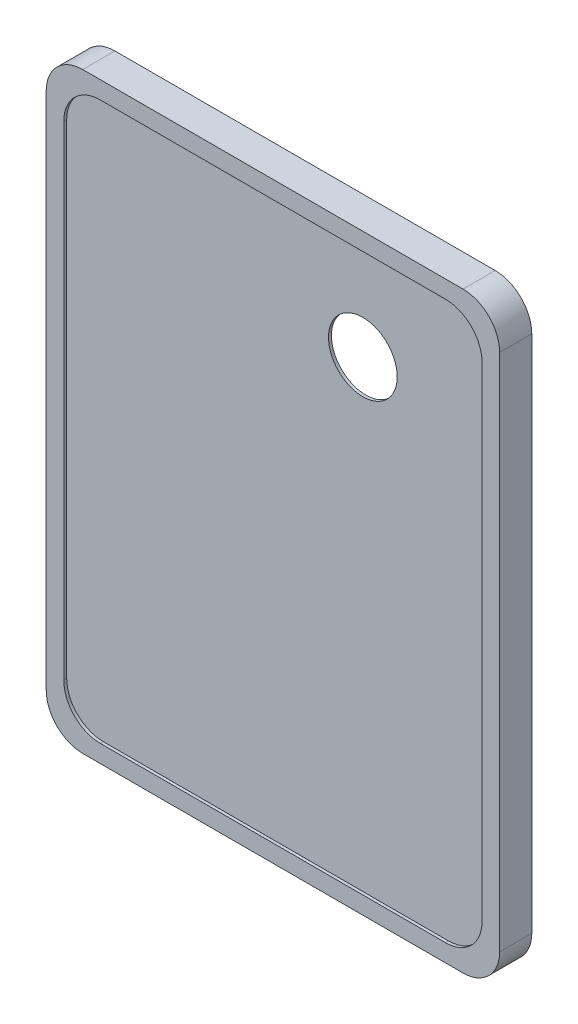
SolidWorks part; units mm, degrees
material "Nickel"
ref_plane "Front Plane" through (0, 0, 0) normal (0, 0, 1) x (1, 0, 0)
ref_plane "Top Plane" through (0, 0, 0) normal (0, 1, 0) x (1, 0, 0)
ref_plane "Right Plane" through (0, 0, 0) normal (1, 0, 0) x (0, 0, -1)
sketch "Sketch1" plane through (0, 0, 0) normal (0, 0, 1) x (1, 0, 0)
  line L1 (-33.02, 51.435) -> (33.02, 51.435)
  line L2 (-39.37, 45.085) -> (-39.37, -45.085)
  line L3 (-33.02, -51.435) -> (33.02, -51.435)
  line L4 (39.37, 45.085) -> (39.37, -45.085)
  line L5 (-39.37, 51.435) -> (39.37, -51.435) construction
  line L6 (-39.37, -51.435) -> (39.37, 51.435) construction
  arc A0 (-39.37, -45.085) -> (-33.02, -51.435) centre (-33.02, -45.085) ccw
  arc A1 (33.02, -51.435) -> (39.37, -45.085) centre (33.02, -45.085) ccw
  arc A2 (39.37, 45.085) -> (33.02, 51.435) centre (33.02, 45.085) ccw
  arc A3 (-33.02, 51.435) -> (-39.37, 45.085) centre (-33.02, 45.085) ccw
  point P0 (0, 0)
  dimension "D3" = 6.35
  dimension "D1" = 102.87
  dimension "D2" = 78.74
extrude "Boss-Extrude1" add sketch "Sketch1" along normal blind 5.588
sketch "Sketch2" plane through (0, 0, 5.588) normal (0, 0, 1) x (1, 0, 0)
  line L0 (39.37, -45.085) -> (39.37, 45.085) construction
  line L1 (-29.972, -48.387) -> (29.972, -48.387)
  line L2 (-36.322, -42.037) -> (-36.322, 42.037)
  line L3 (-29.972, 48.387) -> (29.972, 48.387)
  line L4 (36.322, -42.037) -> (36.322, 42.037)
  line L5 (-36.322, -48.387) -> (36.322, 48.387) construction
  line L6 (-36.322, 48.387) -> (36.322, -48.387) construction
  line L7 (-33.02, -51.435) -> (33.02, -51.435) construction
  arc A0 (-36.322, -42.037) -> (-29.972, -48.387) centre (-29.972, -42.037) ccw
  arc A1 (29.972, -48.387) -> (36.322, -42.037) centre (29.972, -42.037) ccw
  arc A2 (36.322, 42.037) -> (29.972, 48.387) centre (29.972, 42.037) ccw
  arc A3 (-29.972, 48.387) -> (-36.322, 42.037) centre (-29.972, 42.037) ccw
  point P0 (0, 0)
  dimension "D3" = 6.35
  dimension "D1" = 3.048
  dimension "D2" = 3.048
extrude "Cut-Extrude1" cut sketch "Sketch2" against normal blind 0.508
shell "Shell2" thickness 0.508
sketch "Sketch3" plane through (0, 0, 5.08) normal (0, 0, 1) x (1, 0, 0)
  line L0 (39.37, -45.085) -> (39.37, 45.085) construction
  line L1 (33.02, 51.435) -> (-33.02, 51.435) construction
  circle A0 centre (15.113, 32.004) radius 5.969
  dimension "D3" = 11.938
  dimension "D1" = 18.288
  dimension "D2" = 25.4
extrude "Cut-Extrude2" cut sketch "Sketch3" against normal blind 0.508
ref_plane "Plane1" through (39.37, -45.085, 0) normal (0, 1, 0) x (1, 0, 0)
sketch "Sketch5" plane through (39.37, 0, 0) normal (1, 0, 0) x (0, 0, -1)
  line L0 (0, -51.435) -> (2.54, -51.435)
  line L1 (2.54, -51.435) -> (2.54, -50.927)
  line L2 (2.54, -50.927) -> (0, -50.927)
  line L3 (0, -51.435) -> (0, -45.085) construction
  line L4 (0, -50.927) -> (0, -51.435)
  dimension "D1" = 0.508
  dimension "D2" = 2.54
extrude "Boss-Extrude2" add sketch "Sketch5" against normal blind 76.708
sketch "Sketch7" plane through (39.37, 0, 0) normal (1, 0, 0) x (0, 0, -1)
  line L0 (2.54, -50.927) -> (0, -50.927) construction
  circle A0 centre (1.524, -52.197) radius 1.27
  dimension "D1" = 2.54
extrude "Boss-Extrude3" add sketch "Sketch7" against normal blind 76.708
sketch "Sketch8" plane through (39.37, 0, 0) normal (1, 0, 0) x (0, 0, -1)
  line L0 (1.524, -50.927) -> (2.54, -50.927)
  line L1 (2.54, -50.927) -> (2.54, -51.435)
  circle A0 centre (1.524, -52.197) radius 1.27
  line M3 (2.54, -51.435) -> (2.54, -50.927)
  line M4 (2.54, -50.927) -> (0, -50.927)
extrude "Cut-Extrude3" cut sketch "Sketch8" against normal through all contours A0 M3 M4
sketch "Sketch9" plane through (39.37, 0, 0) normal (1, 0, 0) x (0, 0, -1)
  circle A0 centre (1.524, -52.197) radius 1.016
  dimension "D1" = 2.032
extrude "Cut-Extrude4" cut sketch "Sketch9" against normal through all
sketch "Sketch10" plane through (0, 0, 5.588) normal (0, 0, 1) x (1, 0, 0)
  line L0 (-33.02, -51.435) -> (33.02, -51.435) construction
  line L1 (39.37, -51.435) -> (24.892, -51.435)
  line L2 (39.37, -51.435) -> (39.37, -54.461)
  line L3 (39.37, -54.461) -> (24.892, -54.461)
  line L4 (24.892, -51.435) -> (24.892, -54.461)
  line L5 (-37.338, -53.467) -> (-24.638, -53.467)
  line L6 (-37.338, -53.467) -> (-37.338, -51.435)
  line L7 (-37.338, -51.435) -> (-24.638, -51.435)
  line L8 (-24.638, -53.467) -> (-24.638, -51.435)
  line L9 (-37.338, -53.467) -> (39.37, -53.467) construction
  line L10 (-17.526, -53.467) -> (-10.414, -53.467)
  line L11 (-17.526, -53.467) -> (-17.526, -51.435)
  line L12 (-35.5087, -50.927) -> (-37.338, -50.927)
  line L13 (-37.338, -50.927) -> (-37.338, -51.435)
  line L14 (-37.338, -51.435) -> (-33.02, -51.435)
  line L15 (-35.5087, -50.927) -> (-37.338, -50.927)
  line L16 (-37.338, -50.927) -> (-37.338, -51.435)
  line L17 (-37.338, -51.435) -> (-33.02, -51.435)
  line L18 (33.02, -51.435) -> (39.37, -51.435)
  line L19 (39.37, -51.435) -> (39.37, -50.927)
  line L20 (39.37, -50.927) -> (35.5087, -50.927)
  line L21 (33.02, -51.435) -> (39.37, -51.435)
  line L22 (39.37, -51.435) -> (39.37, -50.927)
  line L23 (39.37, -50.927) -> (35.5087, -50.927)
  line L24 (-17.526, -51.435) -> (-10.414, -51.435)
  line L25 (-10.414, -53.467) -> (-10.414, -51.435)
  line L26 (-37.338, -51.435) -> (39.37, -51.435) construction
  line L27 (-3.302, -53.467) -> (3.81, -53.467)
  line L28 (-3.302, -53.467) -> (-3.302, -51.435)
  line L29 (-3.302, -51.435) -> (3.81, -51.435)
  line L30 (3.81, -53.467) -> (3.81, -51.435)
  line L31 (10.922, -53.467) -> (18.034, -53.467)
  line L32 (10.922, -53.467) -> (10.922, -51.435)
  line L33 (10.922, -51.435) -> (18.034, -51.435)
  line L34 (18.034, -53.467) -> (18.034, -51.435)
  arc A1 (-35.5087, -50.927) -> (-33.02, -51.435) centre (-33.02, -45.085) ccw
  arc A2 (-35.5087, -50.927) -> (-33.02, -51.435) centre (-33.02, -45.085) ccw
  arc A3 (33.02, -51.435) -> (35.5087, -50.927) centre (33.02, -45.085) ccw
  arc A4 (33.02, -51.435) -> (35.5087, -50.927) centre (33.02, -45.085) ccw
  point P4 (3.81, -52.451)
  line M35 (-33.02, -51.435) -> (33.02, -51.435)
  dimension "D1" = 14.478
  dimension "D2" = 12.7
  dimension "D5" = 6.858
  dimension "D6" = 7.112
  dimension "D7" = 7.112
  dimension "D8" = 7.112
  dimension "D9" = 7.112
  dimension "D10" = 7.112
  dimension "D11" = 7.112
  dimension "D3" = 0
  dimension "D4" = 0
extrude "Cut-Extrude5" cut sketch "Sketch10" against normal through all contours L10 L25 L11 M35 | L27 L30 L28 M35 | L31 L34 L32 M35 | L4 L3 L2 L1 M35 | L7 L8 L5 L6 | L15 L16 L17 A2 | L23 A4 L21 L22
sketch "Sketch11" plane through (0, -50.927, 0) normal (0, 1, 0) x (1, 0, 0)
  line L1 (24.892, 2.54) -> (35.5087, 2.54)
  line L2 (24.892, 2.54) -> (24.892, 0)
  line L3 (24.892, 0) -> (35.5087, 0)
  line L4 (35.5087, 2.54) -> (35.5087, 0)
  line L5 (-24.638, 2.54) -> (-35.5087, 2.54)
  line L6 (-24.638, 2.54) -> (-24.638, 0)
  line L7 (-24.638, 0) -> (-35.5087, 0)
  line L8 (-35.5087, 2.54) -> (-35.5087, 0)
extrude "Cut-Extrude6" cut sketch "Sketch11" against normal through all
sketch "Sketch12" plane through (0, -50.927, 0) normal (0, 1, 0) x (1, 0, 0)
  line L0 (33.02, 0) -> (-33.02, 0) construction
  line L1 (18.034, 2.54) -> (10.922, 2.54)
  line L2 (18.034, 2.54) -> (18.034, 0)
  line L3 (18.034, 0) -> (10.922, 0)
  line L4 (10.922, 2.54) -> (10.922, 0)
  line L6 (-3.302, 2.54) -> (3.81, 2.54)
  line L7 (-3.302, 2.54) -> (-3.302, 0)
  line L8 (-3.302, 0) -> (3.81, 0)
  line L9 (3.81, 2.54) -> (3.81, 0)
  line L10 (-10.414, 2.54) -> (-17.526, 2.54)
  line L11 (-10.414, 2.54) -> (-10.414, 0)
  line L12 (-10.414, 0) -> (-17.526, 0)
  line L13 (-17.526, 2.54) -> (-17.526, 0)
extrude "Cut-Extrude7" cut sketch "Sketch12" against normal through all
